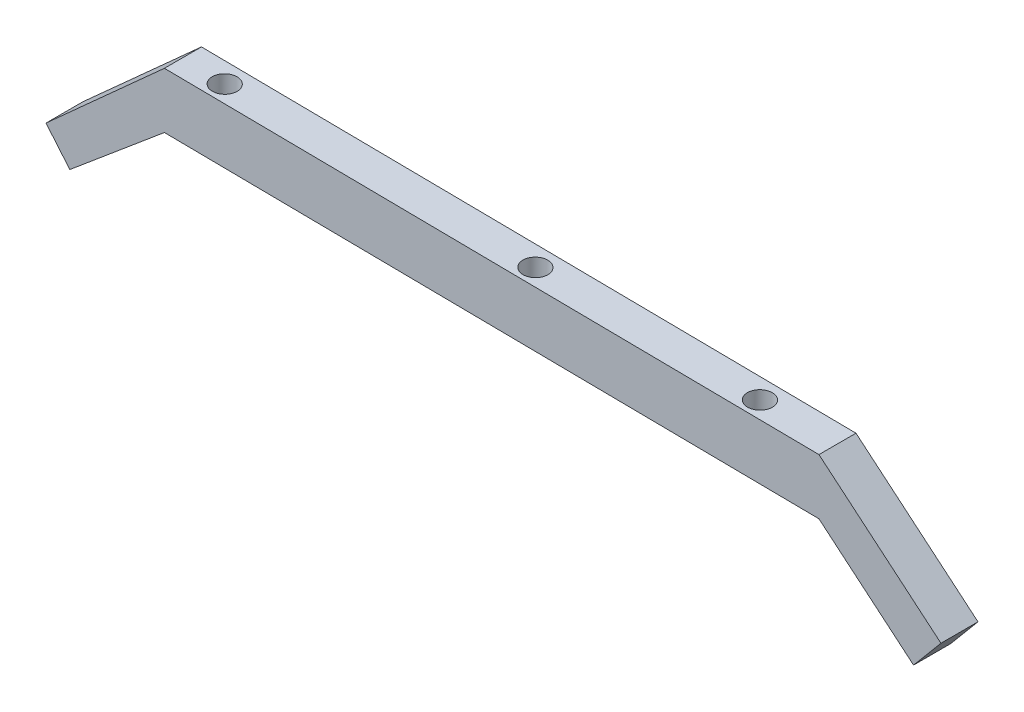
SolidWorks part; units mm, degrees
ref_plane "Front Plane" through (0, 0, 0) normal (0, 0, 1) x (1, 0, 0)
ref_plane "Top Plane" through (0, 0, 0) normal (0, 1, 0) x (1, 0, 0)
ref_plane "Right Plane" through (0, 0, 0) normal (1, 0, 0) x (0, 0, -1)
sketch "Sketch1" plane through (0, 0, 0) normal (0, 0, 1) x (1, 0, 0)
  line L0 (-57.2335, -0.0977) -> (48.7665, -1.275)
  line L1 (-57.2335, -0.0977) -> (-72.5543, -12.9534)
  line L2 (48.7665, -1.275) -> (64.0874, -14.1308)
  line L3 (-72.5543, -12.9534) -> (-76.4111, -8.3571)
  line L4 (64.0874, -14.1308) -> (68.5239, -8.8436)
  line L5 (-76.4111, -8.3571) -> (-57.2335, 8.9122)
  line L6 (-57.2335, 8.9122) -> (48.7665, 7.7348)
  line L7 (48.7665, 7.7348) -> (68.5239, -8.8436)
  line L8 (48.7665, -1.275) -> (48.7665, 7.7348) construction
  line L9 (-57.2335, -0.0977) -> (-57.2335, 8.9122) construction
  point P2 (-57.2335, 4.4073)
extrude "Boss-Extrude1" add sketch "Sketch1" along normal blind 6
sketch "Sketch2" plane through (0.0919, 8.2754, 0) normal (0.0111, 0.9999, 0) x (0.9999, -0.0111, 0)
  circle A0 centre (0, -3.2488) radius 2.0171
  circle A1 centre (36.371, -3.2488) radius 2.0171
  circle A2 centre (-50.3161, -3.2488) radius 2.0171
extrude "Cut-Extrude1" cut sketch "Sketch2" against normal blind 25
